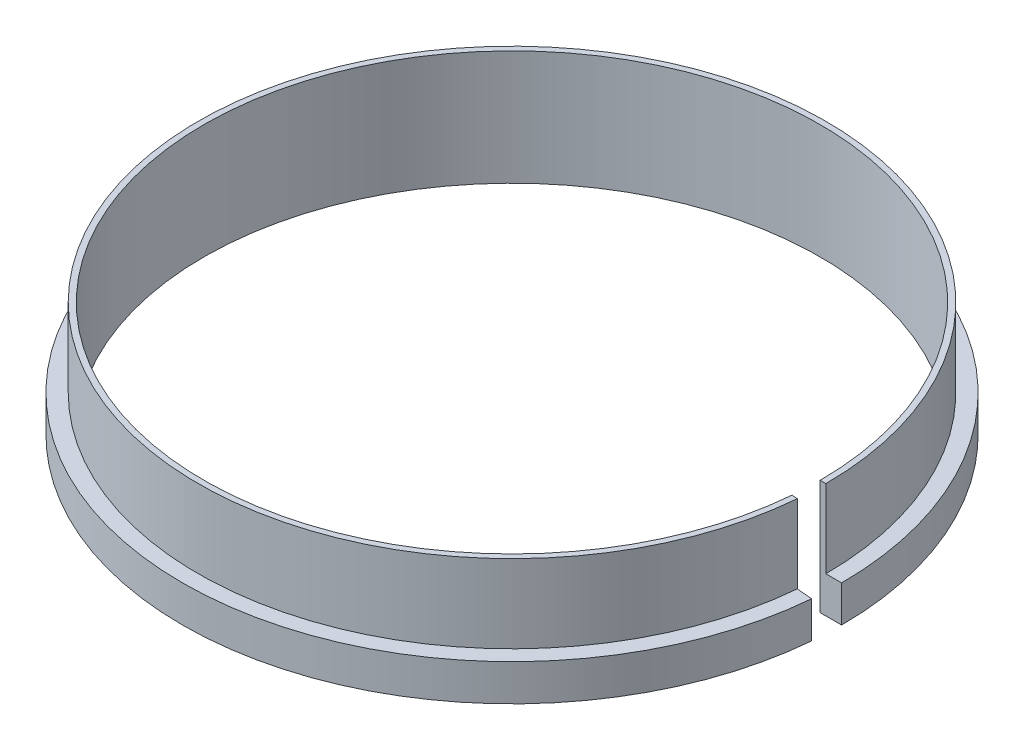
SolidWorks part; units mm, degrees
ref_plane "Front" through (0, 0, 0) normal (0, 0, 1) x (1, 0, 0)
ref_plane "Top" through (0, 0, 0) normal (0, 1, 0) x (1, 0, 0)
ref_plane "Right" through (0, 0, 0) normal (1, 0, 0) x (0, 0, -1)
sketch "Sketch1" plane through (0, 0, 0) normal (0, 0, 1) x (1, 0, 0)
  line L0 (0, 0) -> (0, 8) construction
  line L1 (21.5, 0) -> (21.5, 8)
  line L2 (21.5, 8) -> (21.9, 8)
  line L3 (21.9, 8) -> (21.9, 2.55)
  line L4 (21.9, 2.55) -> (23, 2.55)
  line L5 (23, 2.55) -> (23, 0)
  line L6 (23, 0) -> (21.5, 0)
  point P8 (0, 0)
  point P10 (0, 0)
  dimension "D1" = 8
  dimension "D2" = 0.4
  dimension "D3" = 1.5
  dimension "D4" = 2.55
  dimension "D5" = 43
revolve "Revolve1" add sketch "Sketch1" angle 355 about L0
